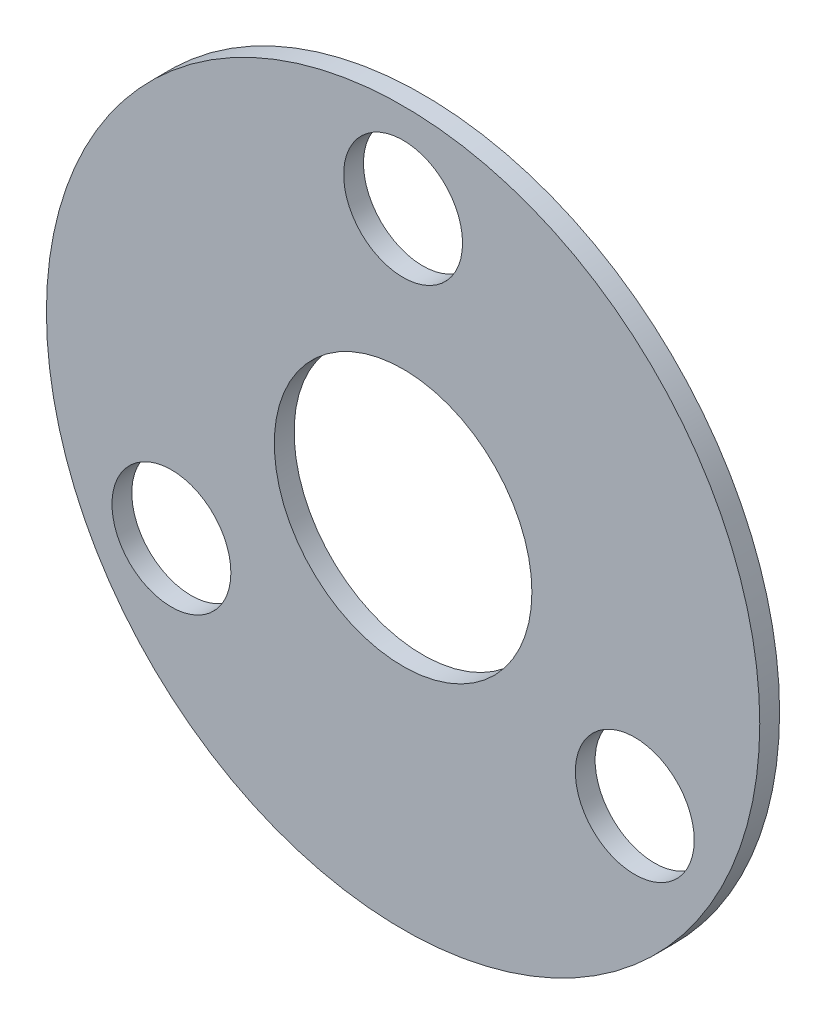
SolidWorks part; units mm, degrees
ref_plane "Alzado" through (0, 0, 0) normal (0, 0, 1) x (1, 0, 0)
ref_plane "Planta" through (0, 0, 0) normal (0, 1, 0) x (1, 0, 0)
ref_plane "Vista lateral" through (0, 0, 0) normal (1, 0, 0) x (0, 0, -1)
sketch "Croquis1" plane through (0, 0, 0) normal (0, 0, 1) x (1, 0, 0)
  circle A0 centre (0, 0) radius 18
  point P0 (0, 0)
  dimension "D3" = 36
extrude "Saliente-Extruir2" add sketch "Croquis1" along normal blind 1
sketch "Croquis5" plane through (0, 0, 1) normal (0, 0, 1) x (1, 0, 0)
  circle A0 centre (0, 0) radius 13.5
  circle A1 centre (0, 13.5) radius 3
  circle A2 centre (11.6913, -6.75) radius 3
  circle A3 centre (-11.6913, -6.75) radius 3
  circle A4 centre (0, 0) radius 6.5
  point P12 (0, 0)
  dimension "D1" = 27
  dimension "D2" = 6
  dimension "D4" = 13
  dimension "D3" = 3
extrude "Cortar-Extruir3" cut sketch "Croquis5" against normal blind 1 contours A1 | A3 | A2 | A4
